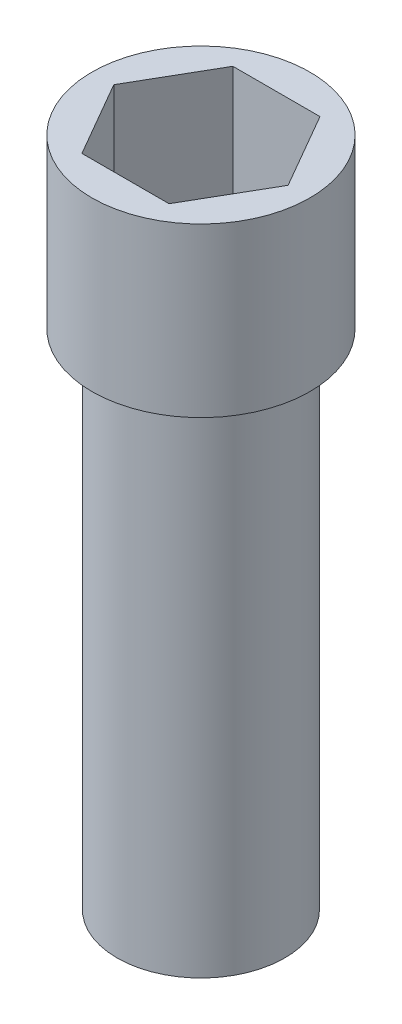
SolidWorks part; units mm, degrees
ref_plane "Front Plane" through (0, 0, 0) normal (0, 0, 1) x (1, 0, 0)
ref_plane "Top Plane" through (0, 0, 0) normal (0, 1, 0) x (1, 0, 0)
ref_plane "Right Plane" through (0, 0, 0) normal (1, 0, 0) x (0, 0, -1)
sketch "Sketch1" plane through (0, 0, 0) normal (0, 1, 0) x (1, 0, 0)
  circle A0 centre (0, 0) radius 5
  dimension "D1" = 10
extrude "Boss-Extrude1" add sketch "Sketch1" along normal blind 30
sketch "Sketch2" plane through (0, 30, 0) normal (0, 1, 0) x (1, 0, 0)
  circle A0 centre (0, 0) radius 6.5
  dimension "D1" = 13
extrude "Boss-Extrude2" add sketch "Sketch2" along normal blind 2
sketch "Sketch3" plane through (0, 32, 0) normal (0, 1, 0) x (1, 0, 0)
  line L1 (5.1962, 0) -> (2.5981, 4.5)
  line L2 (2.5981, 4.5) -> (-2.5981, 4.5)
  line L3 (-2.5981, 4.5) -> (-5.1962, 0)
  line L4 (-5.1962, 0) -> (-2.5981, -4.5)
  line L5 (-2.5981, -4.5) -> (2.5981, -4.5)
  line L6 (2.5981, -4.5) -> (5.1962, 0)
  circle A0 centre (0, 0) radius 4.5 construction
  circle A1 centre (0, 0) radius 6.5
  circle A2 centre (0, 0) radius 6.5
  point P0 (0, 0)
  dimension "D2" = 9
  dimension "D1" = 0
extrude "Boss-Extrude3" add sketch "Sketch3" along normal blind 8
